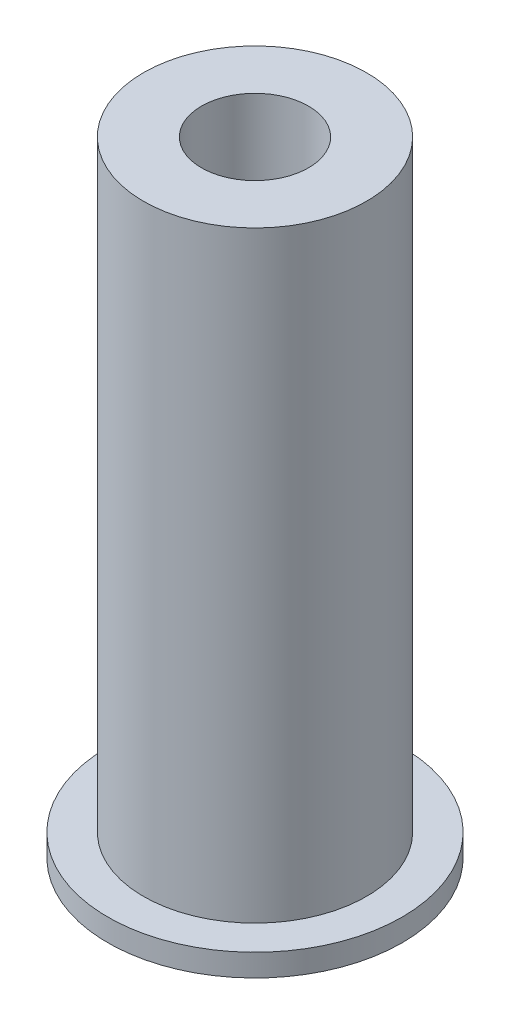
SolidWorks part; units mm, degrees
material "ABS"
ref_plane "Front Plane" through (0, 0, 0) normal (0, 0, 1) x (1, 0, 0)
ref_plane "Top Plane" through (0, 0, 0) normal (0, 1, 0) x (1, 0, 0)
ref_plane "Right Plane" through (0, 0, 0) normal (1, 0, 0) x (0, 0, -1)
sketch "Sketch1" plane through (0, 0, 0) normal (0, 0, 1) x (1, 0, 0)
  line L0 (-6.25, -33.75) -> (-6.25, 0)
  line L2 (0, 0) -> (0, -38.7973) construction
  line L3 (-6.25, 0) -> (-3, 0)
  line L4 (-6.25, -33.75) -> (-8.25, -33.75)
  line L5 (-8.25, -33.75) -> (-8.25, -35)
  line L7 (-8.25, -35) -> (-5, -35)
  line L8 (-3, 0) -> (-3, -17)
  line L9 (-3, -17) -> (-5, -17)
  line L10 (-5, -17) -> (-5, -35)
  line L11 (0, -22.722) -> (0, -0.722) construction
  dimension "D1" = 1.25
  dimension "D2" = 5
  dimension "D3" = 35
  dimension "D4" = 3.25
  dimension "D5" = 1.25
  dimension "D6" = 6
  dimension "D7" = 18
revolve "Revolve1" add sketch "Sketch1" angle 360 about L2
